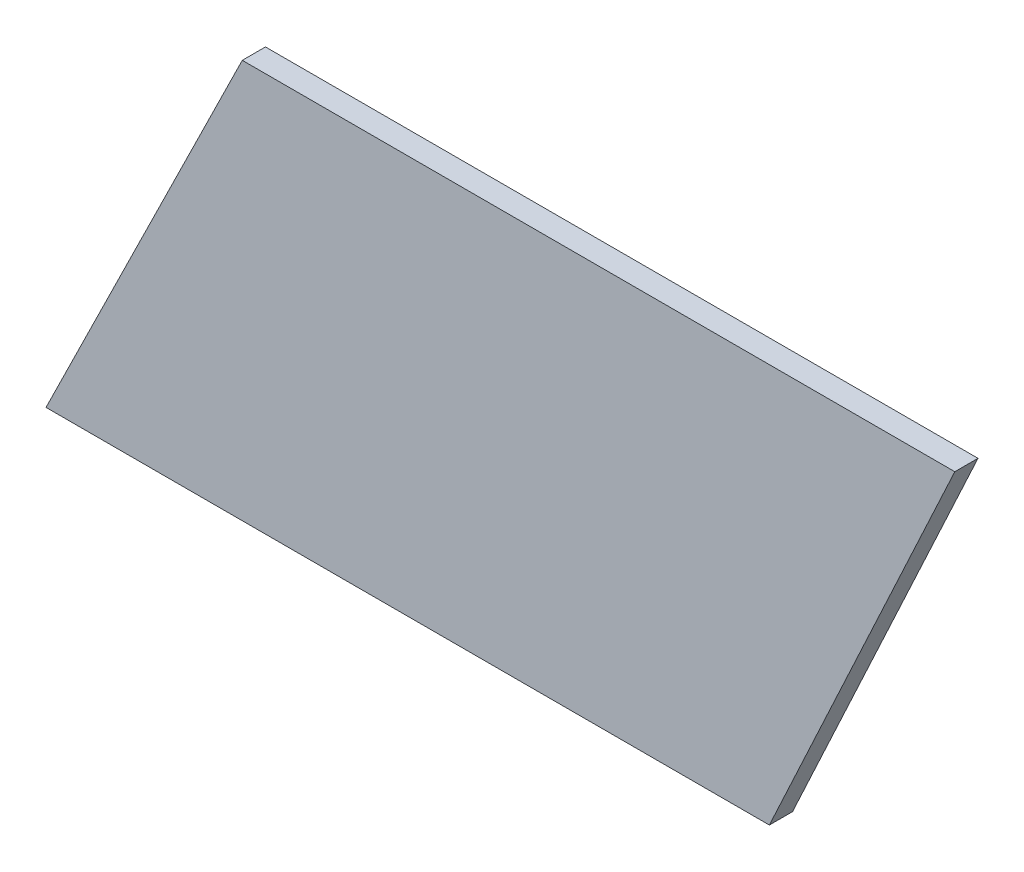
SolidWorks part; units mm, degrees
ref_plane "Front Plane" through (0, 0, 0) normal (0, 0, 1) x (1, 0, 0)
ref_plane "Top Plane" through (0, 0, 0) normal (0, 1, 0) x (1, 0, 0)
ref_plane "Right Plane" through (0, 0, 0) normal (1, 0, 0) x (0, 0, -1)
sketch "Sketch1" plane through (0, 0, 0) normal (0, 0, 1) x (1, 0, 0)
  line L0 (0, 15.245) -> (12, 41.045)
  line L1 (12, 41.045) -> (-34.1, 41.045)
  line L2 (-34.1, 41.045) -> (-46.8, 15.245)
  line L3 (-46.8, 15.245) -> (0, 15.245)
  dimension "D1" = 46.8
  dimension "D2" = 46.1
  dimension "D3" = 25.8
  dimension "D4" = 12.7
  dimension "D5" = 15.245
extrude "Boss-Extrude1" add sketch "Sketch1" along normal mid plane 1.5
sketch "Sketch2" plane through (0, 0, 0) normal (1, 0, 0) x (0, 0, -1)
  circle A0 centre (0, 0) radius 15.265
extrude "Cut-Extrude1" cut sketch "Sketch2" against normal through all
